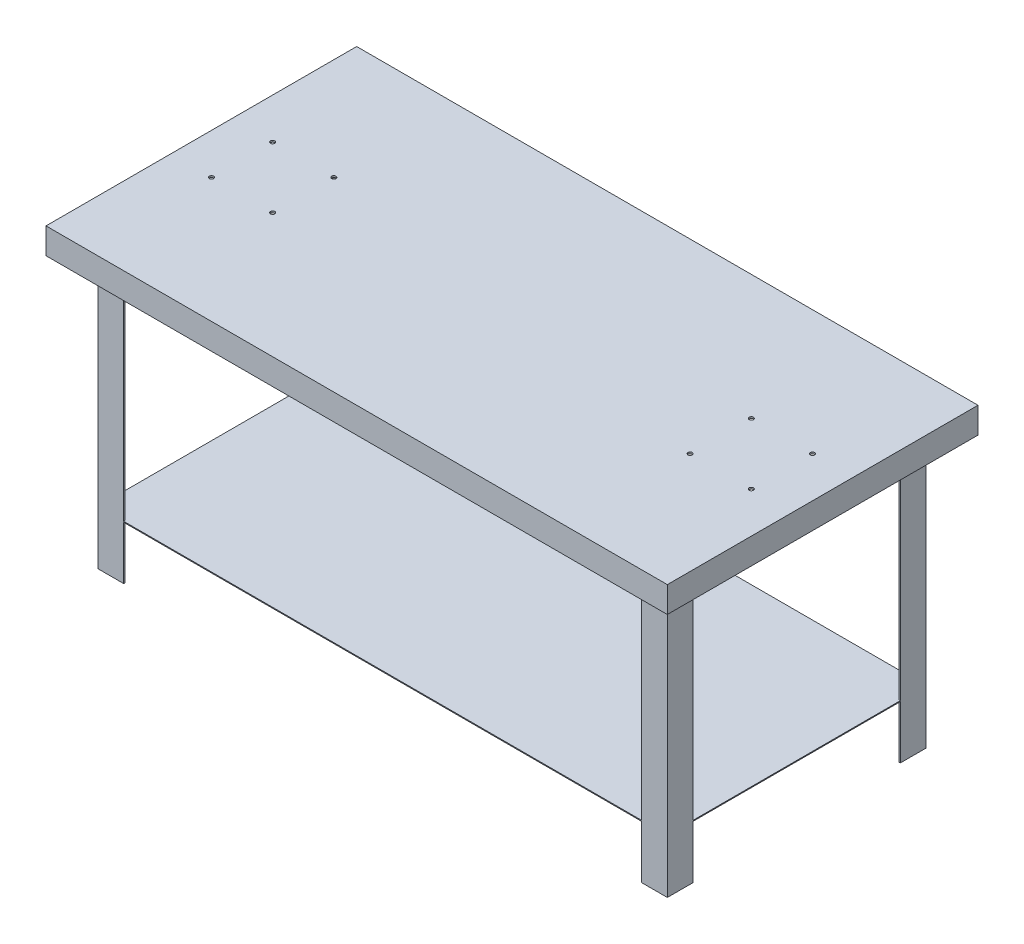
SolidWorks part; units mm, degrees
material "1023 Carbon Steel Sheet (SS)"
ref_plane "Front Plane" through (0, 0, 0) normal (0, 0, 1) x (1, 0, 0)
ref_plane "Top Plane" through (0, 0, 0) normal (0, 1, 0) x (1, 0, 0)
ref_plane "Right Plane" through (0, 0, 0) normal (1, 0, 0) x (0, 0, -1)
sketch "Sketch1" plane through (0, 0, 0) normal (1, 0, 0) x (0, 0, -1)
  line L0 (0, -1534.4769) -> (0, 75189.3682) construction
  line L1 (-457.2, 0) -> (457.2, 0)
  line L2 (457.2, 0) -> (457.2, -76.2)
  line L3 (457.2, -76.2) -> (381, -76.2)
  line L4 (-457.2, -76.2) -> (-381, -76.2)
  line L5 (-457.2, 0) -> (-457.2, -76.2)
  line L6 (-452.4375, -71.4375) -> (-381, -71.4375)
  line L7 (-452.4375, -4.7625) -> (-452.4375, -71.4375)
  line L8 (-452.4375, -4.7625) -> (452.4375, -4.7625)
  line L9 (452.4375, -4.7625) -> (452.4375, -71.4375)
  line L10 (452.4375, -71.4375) -> (381, -71.4375)
  line L11 (-381, -71.4375) -> (-381, -76.2)
  line L12 (381, -71.4375) -> (381, -76.2)
  point P10 (0, 0)
  dimension "D1" = 76.2
  dimension "D2" = 76.2
  dimension "D3" = 914.4
  dimension "D4" = 4.7625
extrude "Boss-Extrude1" add sketch "Sketch1" along normal mid plane 1828.8
sketch "Sketch2" plane through (0, 0, 0) normal (0, 0, 1) x (1, 0, 0)
  line L0 (0, -1000) -> (0, 49000) construction
  line L1 (-914.4, 0) -> (-914.4, -76.2)
  line L2 (-914.4, -76.2) -> (-838.2, -76.2)
  line L3 (914.4, -76.2) -> (-914.4, -76.2) construction
  line L4 (-838.2, -76.2) -> (-838.2, -71.4375)
  line L5 (-838.2, -71.4375) -> (-909.6375, -71.4375)
  line L6 (-909.6375, -71.4375) -> (-909.6375, 0)
  line L7 (914.4, 0) -> (-914.4, 0) construction
  line L8 (-909.6375, 0) -> (-914.4, 0)
  line L9 (909.6375, 0) -> (914.4, 0)
  line L10 (909.6375, -71.4375) -> (909.6375, 0)
  line L11 (838.2, -71.4375) -> (909.6375, -71.4375)
  line L12 (838.2, -76.2) -> (838.2, -71.4375)
  line L13 (914.4, -76.2) -> (838.2, -76.2)
  line L14 (914.4, 0) -> (914.4, -76.2)
  dimension "D1" = 4.7625
extrude "Boss-Extrude2" add sketch "Sketch2" along normal mid plane 914.4
sketch "Sketch3" plane through (0, 0, 0) normal (0, 1, 0) x (1, 0, 0)
  line L1 (-840, 90) -> (-660, 90)
  line L2 (-840, 90) -> (-840, -90)
  line L3 (-840, -90) -> (-660, -90)
  line L4 (-660, 90) -> (-660, -90)
  line L5 (-750, -90) -> (-750, 90) construction
  line L6 (-840, 0) -> (-660, 0) construction
  point P0 (-750, 0)
  dimension "D1" = 180
  dimension "D2" = 750
split line "Split Line1" [suppressed]
sketch "Sketch4" plane through (0, -4.7625, 0) normal (0, -1, 0) x (1, 0, 0)
  line L0 (0, -1000) -> (0, 49000) construction
  line L1 (-1000, 0) -> (49000, 0) construction
  line L2 (-762, 381) -> (-838.2, 381)
  line L3 (838.2, 381) -> (-838.2, 381) construction
  line L4 (-838.2, 381) -> (-838.2, 304.8)
  line L5 (-838.2, 381) -> (-838.2, -381) construction
  line L6 (-838.2, 304.8) -> (-833.646, 304.8)
  line L7 (-833.646, 304.8) -> (-833.646, 376.446)
  line L8 (-833.646, 376.446) -> (-762, 376.446)
  line L9 (-762, 376.446) -> (-762, 381)
  line L10 (-833.646, -376.446) -> (-762, -376.446)
  line L11 (-833.646, -304.8) -> (-833.646, -376.446)
  line L12 (-838.2, -304.8) -> (-833.646, -304.8)
  line L13 (-838.2, -381) -> (-838.2, -304.8)
  line L14 (-762, -381) -> (-838.2, -381)
  line L15 (-762, -376.446) -> (-762, -381)
  line L16 (833.646, -304.8) -> (833.646, -376.446)
  line L17 (838.2, -304.8) -> (833.646, -304.8)
  line L18 (838.2, -381) -> (838.2, -304.8)
  line L19 (762, -381) -> (838.2, -381)
  line L20 (762, -376.446) -> (762, -381)
  line L21 (833.646, -376.446) -> (762, -376.446)
  line L22 (833.646, 376.446) -> (762, 376.446)
  line L23 (833.646, 304.8) -> (833.646, 376.446)
  line L24 (838.2, 304.8) -> (833.646, 304.8)
  line L25 (838.2, 381) -> (838.2, 304.8)
  line L26 (762, 381) -> (838.2, 381)
  line L27 (762, 376.446) -> (762, 381)
  dimension "D1" = 4.554
  dimension "D2" = 76.2
extrude "Boss-Extrude3" add sketch "Sketch4" along normal offset from surface (868.9975 mm away) 873.76 up to face at (0, 0, 0)
sketch "Sketch5" plane through (0, -4.7625, 0) normal (0, -1, 0) x (1, 0, 0)
  line L1 (-838.2, 381) -> (838.2, 381)
  line L2 (-838.2, 381) -> (-838.2, -381)
  line L3 (-838.2, -381) -> (838.2, -381)
  line L4 (838.2, 381) -> (838.2, -381)
extrude "Boss-Extrude4" add sketch "Sketch5" against normal blind 2.657 from offset 712.7875
sketch "Sketch6" plane through (0, 0, 0) normal (0, 1, 0) x (1, 0, 0)
  line L0 (0, -1000) -> (0, 49000) construction
  line L1 (-914.4, 457.2) -> (-914.4, -457.2) construction
  line L3 (-794.4, -90) -> (-614.4, -90) construction
  line L4 (-794.4, -90) -> (-794.4, 90) construction
  line L5 (-794.4, 90) -> (-614.4, 90) construction
  line L6 (-614.4, -90) -> (-614.4, 90) construction
  line L7 (-704.4, 90) -> (-704.4, -90) construction
  line L8 (-794.4, 0) -> (-614.4, 0) construction
  circle A0 centre (-794.4, 90) radius 6.35
  circle A1 centre (-614.4, 90) radius 6.35
  circle A2 centre (-794.4, -90) radius 6.35
  circle A3 centre (-614.4, -90) radius 6.35
  circle A4 centre (614.4, -90) radius 6.35
  circle A5 centre (794.4, -90) radius 6.35
  circle A6 centre (794.4, 90) radius 6.35
  circle A7 centre (614.4, 90) radius 6.35
  point P4 (-704.4, 0)
  dimension "D3" = 12.7
  dimension "D1" = 180
  dimension "D2" = 704.4
  dimension "D4" = 120
extrude "Cut-Extrude1" cut sketch "Sketch6" against normal blind 10
sketch "Sketch7" plane through (0, 0, 0) normal (1, 0, 0) x (0, 0, -1)
  line L0 (452.4375, -4.7625) -> (-452.4375, -4.7625)
  line L1 (452.4375, -4.7625) -> (-452.4375, -4.7625) construction
  line L2 (0, -1000) -> (0, 49000) construction
  line L3 (63.1726, -4.7625) -> (50.8, -4.7625)
  line L4 (50.8, -4.7625) -> (0, -66.0384)
  line L5 (63.1726, -4.7625) -> (0, -80.9625)
  line L6 (-50.8, -4.7625) -> (0, -66.0384)
  line L7 (-63.1726, -4.7625) -> (0, -80.9625)
  line L8 (-63.1726, -4.7625) -> (-50.8, -4.7625)
  dimension "D1" = 101.6
  dimension "D2" = 76.2
  dimension "D3" = 9.525
extrude "Boss-Extrude5" add sketch "Sketch7" along normal mid plane 1558
